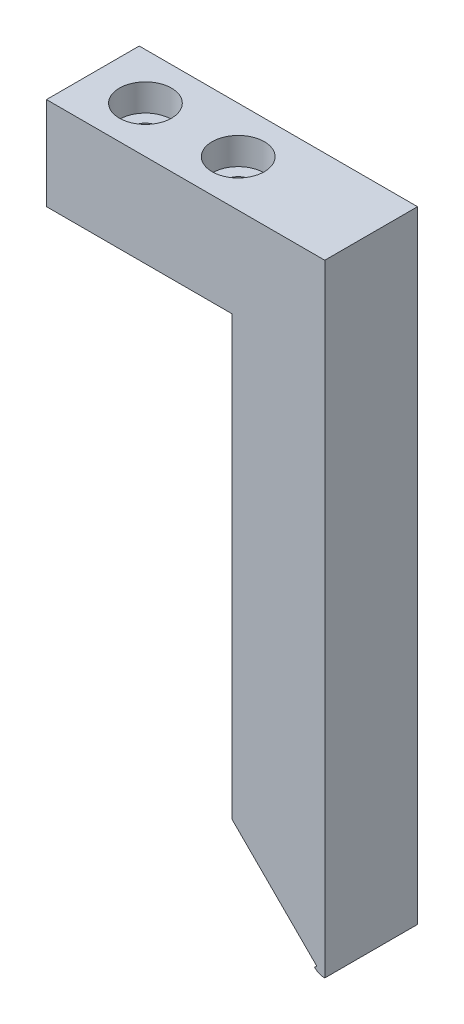
SolidWorks part; units mm, degrees
ref_plane "Front" through (0, 0, 0) normal (0, 0, 1) x (1, 0, 0)
ref_plane "Top" through (0, 0, 0) normal (0, 1, 0) x (1, 0, 0)
ref_plane "Right" through (0, 0, 0) normal (1, 0, 0) x (0, 0, -1)
sketch "Sketch1" plane through (0, 0, 0) normal (0, 0, 1) x (1, 0, 0)
  line L1 (0, 0) -> (38.1, 0)
  line L2 (0, 0) -> (0, -85.1)
  line L3 (0, -85.1) -> (38.1, -85.1)
  line L4 (38.1, 0) -> (38.1, -85.1)
  dimension "D1" = 85.1
  dimension "D2" = 38.1
extrude "Boss-Extrude1" add sketch "Sketch1" along normal mid plane 12.7
sketch "Sketch2" plane through (0, 0, 6.35) normal (0, 0, 1) x (1, 0, 0)
  line L0 (38.1, 0) -> (0, 0) construction
  line L1 (0, -85.1) -> (25.4, -85.1)
  line L2 (0, -85.1) -> (0, -12.7)
  line L3 (0, -12.7) -> (25.4, -12.7)
  line L4 (25.4, -85.1) -> (25.4, -12.7)
  dimension "D1" = 25.4
  dimension "D2" = 12.7
extrude "Cut-Extrude1" cut sketch "Sketch2" against normal through all
hole_wizard "CBORE for #6 Socket Head Cap Screw1" positions "Sketch8" profile "Sketch7" counterbore size "#6" standard "Ansi Inch" end condition through all
sketch "Sketch8" plane through (0, 0, 0) normal (0, 1, 0) x (-1, 0, 0)
  line L0 (50, 0) -> (-50, 0) construction
  line L1 (0, 6.35) -> (0, -6.35) construction
  point P0 (-7.2, 0)
  point P1 (-19.9, 0)
  dimension "D1" = 7.2
  dimension "D2" = 12.7
sketch "Sketch7" plane through (7.2, 0, 0) normal (1, 0, 0) x (0, 0, 1)
  line L0 (0, 0) -> (0, 85.1)
  line L1 (0, 85.1) -> (1.8986, 85.1)
  line L3 (1.8986, 85.1) -> (1.8987, 3.7052)
  line L4 (1.8987, 3.7052) -> (3.5725, 3.7052)
  line L5 (3.5725, 3.7052) -> (3.5725, 0)
  line L7 (3.5725, 0) -> (0, 0)
  line L11 (0, -6.35) -> (0, 107.95) construction
  dimension "Thru Hole Dia." = 3.7973
  dimension "Thru Hole Depth" = 85.1
  dimension "C'Bore Dia." = 7.145
  dimension "C'Bore Depth" = 3.7052
sketch "Sketch9" plane through (0, 0, 6.35) normal (0, 0, 1) x (1, 0, 0)
  line L0 (25.4, -84.8) -> (36.6859, -84.8)
  line L1 (25.4, -85.1) -> (25.4, -12.7) construction
  line L3 (37.4, -85.1) -> (38.1, -85.1)
  line L4 (25.4, -84.8) -> (25.4, -88.1)
  line L5 (25.4, -88.1) -> (38.1, -88.1)
  line L6 (38.1, -88.1) -> (38.1, -85.1)
  line L7 (25.4, -85.1) -> (38.1, -85.1) construction
  arc A0 (37.4, -85.1) -> (36.6859, -84.8) centre (37.4, -84.1) cw
  dimension "D1" = 1
  dimension "D2" = 0.7
  dimension "D3" = 0.3
  dimension "D4" = 3
extrude "Cut-Extrude2" cut sketch "Sketch9" against normal through all
sketch "Sketch22" plane through (0, -84.8, 0) normal (0, -1, 0) x (1, 0, 0)
  line L0 (36.4359, 8.7839) -> (36.4359, -9.0734)
  line L1 (36.6859, -6.35) -> (36.6859, 6.35) construction
  dimension "D1" = 0.25
ref_plane "Plane2" through (-24.1821, -24.1821, 0) normal (-0.7071, -0.7071, 0) x (0.7071, -0.7071, 0)
ref_plane "Plane3" through (-23.8992, -23.8992, 0) normal (-0.7071, -0.7071, 0) x (0, 0, 1)
sketch "Sketch23" plane through (0, 0, 6.35) normal (0, 0, 1) x (1, 0, 0)
  line L0 (36.4359, -84.8) -> (37.5609, -83.675)
  line L1 (-28.5712, -19.7929) -> (-19.7929, -28.5712) construction
  line L2 (36.6859, -84.8) -> (25.4, -84.8) construction
  line L3 (-28.2884, -19.5101) -> (-19.5101, -28.2884) construction
  point P6 (36.7187, -84.5172)
sketch "Sketch24" plane through (0, 0, 6.35) normal (0, 0, 1) x (1, 0, 0)
  line L0 (38.1, -85.1) -> (38, -85.1)
  line L1 (37.4, -85.1) -> (38.1, -85.1) construction
  line L2 (36.7187, -84.5172) -> (37.0015, -84.2343)
  line L3 (37.0015, -84.2343) -> (25.4, -72.6328)
  line L4 (36.6859, -84.8) -> (25.4, -84.8) construction
  line L5 (25.4, -84.8) -> (25.4, -12.7) construction
  line L6 (25.4, -72.6328) -> (22.8948, -72.6328)
  line L7 (22.8948, -72.6328) -> (22.8948, -86.8623)
  line L8 (22.8948, -86.8623) -> (38.1, -86.8623)
  line L9 (38.1, -86.8623) -> (38.1, -85.1)
  arc A0 (38, -85.1) -> (36.7187, -84.5172) centre (38, -83.4002) cw
  dimension "D2" = 1.6998
  dimension "D1" = 0.1
  dimension "D3" = 45
  dimension "D4" = 0.4
extrude "Cut-Extrude7" cut sketch "Sketch24" against normal up to next
fillet "Fillet1" [suppressed] radius 0.17
fillet "Fillet2" [suppressed] radius 0.1
sketch "Sketch18" plane through (25.4, 0, 0) normal (-1, 0, 0) x (0, 0, 1)
  line L0 (0, -67.825) -> (0, -75.0687) construction
sketch "Sketch25" plane through (60.6179, -60.6179, 0) normal (-0.7071, 0.7071, 0) x (0, 0, 1)
  line L0 (0, -33.042) -> (0, -36.8946)
hole_wizard "#4-40 Tapped Hole1" positions "Sketch11" profile "Sketch10" tap size "#4-40" standard "Ansi Inch"
sketch "Sketch11" plane through (-19.2889, -27.9439, 153.6945) normal (-0.7071, -0.7071, 0) x (0.7071, -0.7071, 0)
  line L7 (71.6264, -153.6945) -> (71.6264, -160.0445) construction
  line L19 (63.1996, -153.6945) -> (79.6067, -153.6945) construction
  line L31 (63.1996, -160.0445) -> (79.6067, -160.0445) construction
  point P0 (71.6264, -150.5195)
  point P25 (71.6264, -156.8695)
  point P107 (71.6264, -156.8695)
  dimension "D1" = 7.9803
sketch "Sketch10" plane through (31.3586, -78.5914, 3.175) normal (0, 0, 1) x (0.7071, -0.7071, 0)
  line L0 (0, 0) -> (0, 6.8592)
  line L1 (0, 6.8592) -> (1.1303, 6.18)
  line L2 (1.1303, 6.18) -> (1.1303, 0)
  line L5 (1.1303, 0) -> (0, 0)
  line L10 (0, 6.8592) -> (-1.1303, 6.18) construction
  line L11 (0, -6.35) -> (0, 107.95) construction
  dimension "Tap Drill Dia." = 2.2606
  dimension "Tap Drill Depth" = 6.18
  dimension "Drill Angle" = 118
cosmetic thread "Hole Thread17" parameters "D1"=4.27, "D2"=2.8448
cosmetic thread "Hole Thread18" parameters "D1"=4.27, "D2"=2.8448
